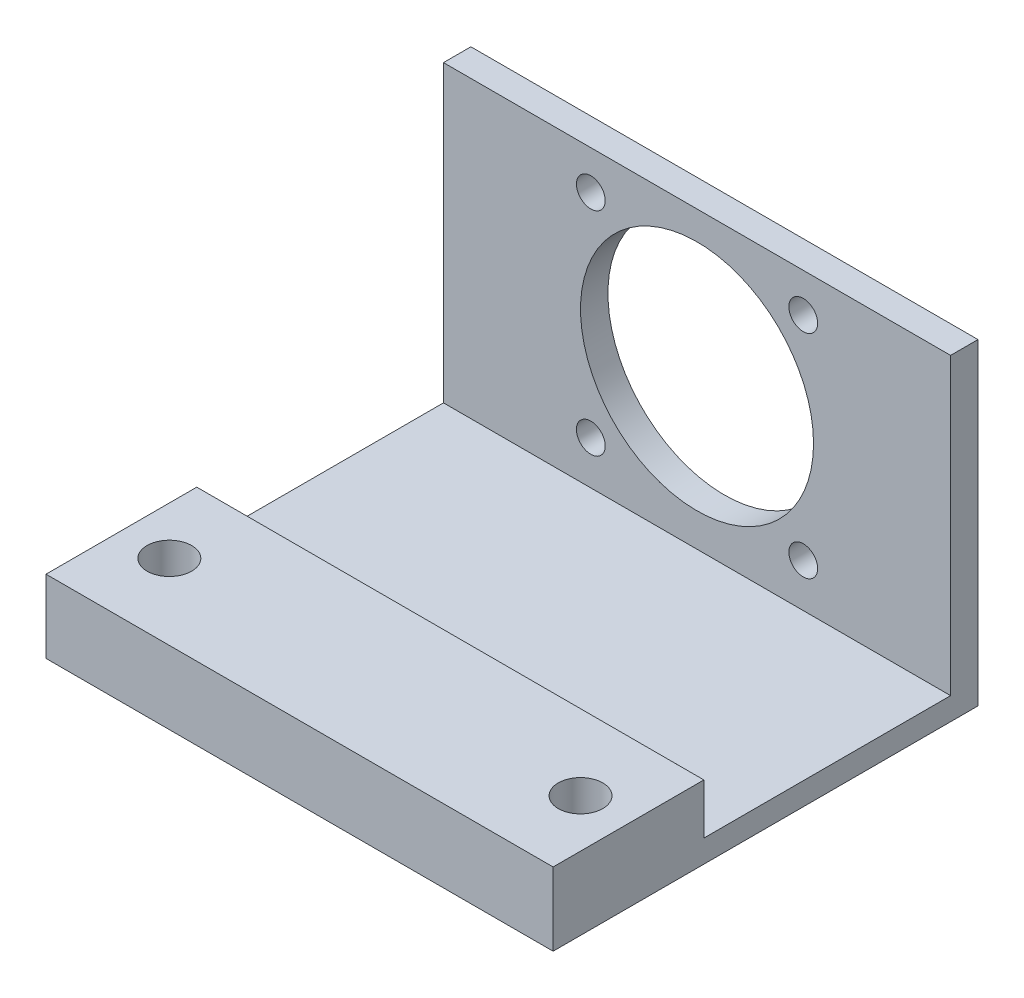
SolidWorks part; units mm, degrees
ref_plane "Alzado" through (0, 0, 0) normal (0, 0, 1) x (1, 0, 0)
ref_plane "Planta" through (0, 0, 0) normal (0, 1, 0) x (1, 0, 0)
ref_plane "Vista lateral" through (0, 0, 0) normal (1, 0, 0) x (0, 0, -1)
sketch "Croquis1" plane through (0, 0, 0) normal (0, 0, 1) x (1, 0, 0)
  line L13 (37, 21.15) -> (-37, 21.15)
  line L14 (-37, 21.15) -> (-37, -25.15)
  line L15 (37, 21.15) -> (37, -25.15)
  line L16 (37, -25.15) -> (-37, -25.15)
  circle A0 centre (0, 0) radius 17
  circle A1 centre (-15.5, -15.5) radius 2.1
  circle A2 centre (-15.5, 15.5) radius 2.1
  circle A3 centre (15.5, -15.5) radius 2.1
  circle A4 centre (15.5, 15.5) radius 2.1
  dimension "D1" = 31
  dimension "D3" = 4.2
  dimension "D6" = 34
  dimension "D2" = 31
  dimension "D4" = 74
  dimension "D5" = 46.3
extrude "Saliente-Extruir1" add sketch "Croquis1" along normal blind 4
sketch "Croquis5" plane through (-37, 0, 0) normal (-1, 0, 0) x (0, 0, 1)
  line L0 (4, -25.15) -> (62, -25.15)
  line L1 (4, -21.85) -> (40, -21.85)
  line L2 (4, -21.85) -> (4, -25.15)
  line L3 (62, -25.15) -> (62, -14.5)
  line L4 (62, -14.5) -> (40, -14.5)
  line L5 (40, -14.5) -> (40, -21.85)
  dimension "D1" = 7.35
  dimension "D2" = 10.65
  dimension "D3" = 36
  dimension "D4" = 58
extrude "Saliente-Extruir3" add sketch "Croquis5" against normal up to vertex (74 mm away)
sketch "Croquis6" plane through (0, -14.5, 0) normal (0, 1, 0) x (1, 0, 0)
  line L0 (37, -62) -> (-37, -62) construction
  line L1 (-37, -62) -> (-37, -40) construction
  circle A1 centre (-30, -51) radius 3.25
  circle A2 centre (30, -51) radius 3.25
  dimension "D1" = 6.5
  dimension "D2" = 6.5
  dimension "D3" = 60
  dimension "D4" = 11
  dimension "D5" = 7
extrude "Cortar-Extruir2" cut sketch "Croquis6" against normal up to next
